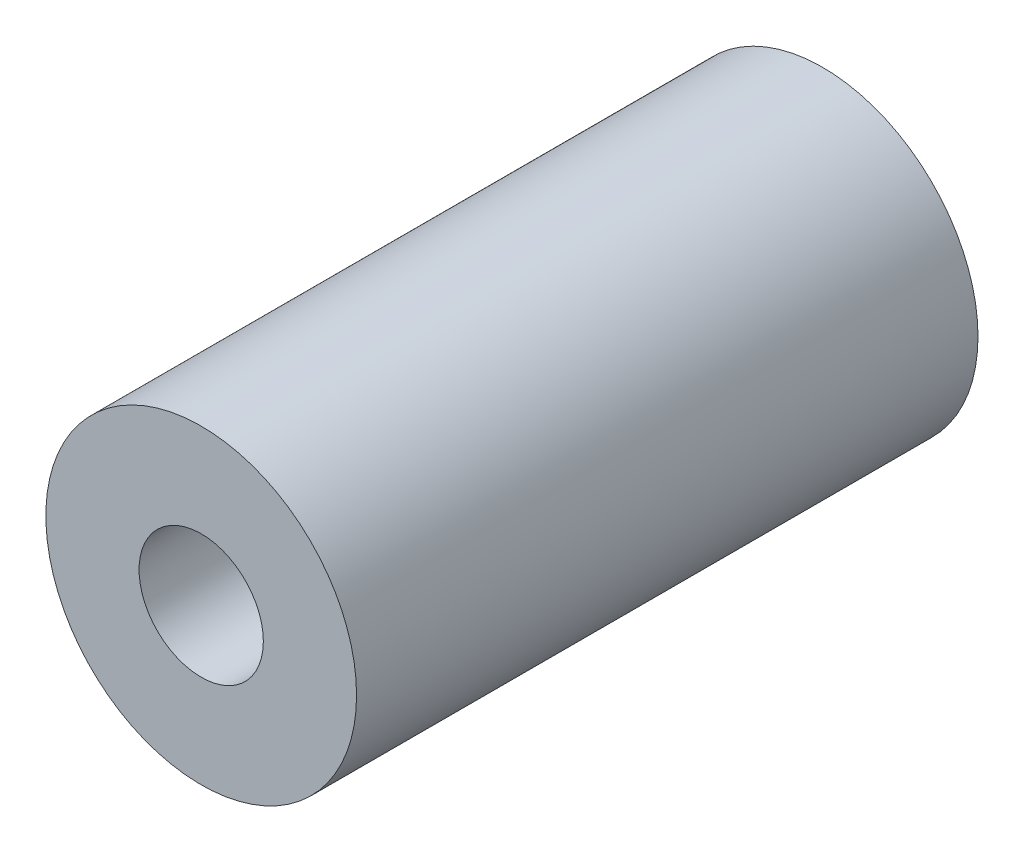
SolidWorks part; units mm, degrees
ref_plane "Front Plane" through (0, 0, 0) normal (0, 0, 1) x (1, 0, 0)
ref_plane "Top Plane" through (0, 0, 0) normal (0, 1, 0) x (1, 0, 0)
ref_plane "Right Plane" through (0, 0, 0) normal (1, 0, 0) x (0, 0, -1)
sketch "Sketch1" plane through (0, 0, 0) normal (0, 0, 1) x (1, 0, 0)
  circle A0 centre (0, 0) radius 5
  circle A1 centre (0, 0) radius 2
  dimension "D1" = 10
  dimension "D2" = 4
extrude "Boss-Extrude1" add sketch "Sketch1" along normal mid plane 20
